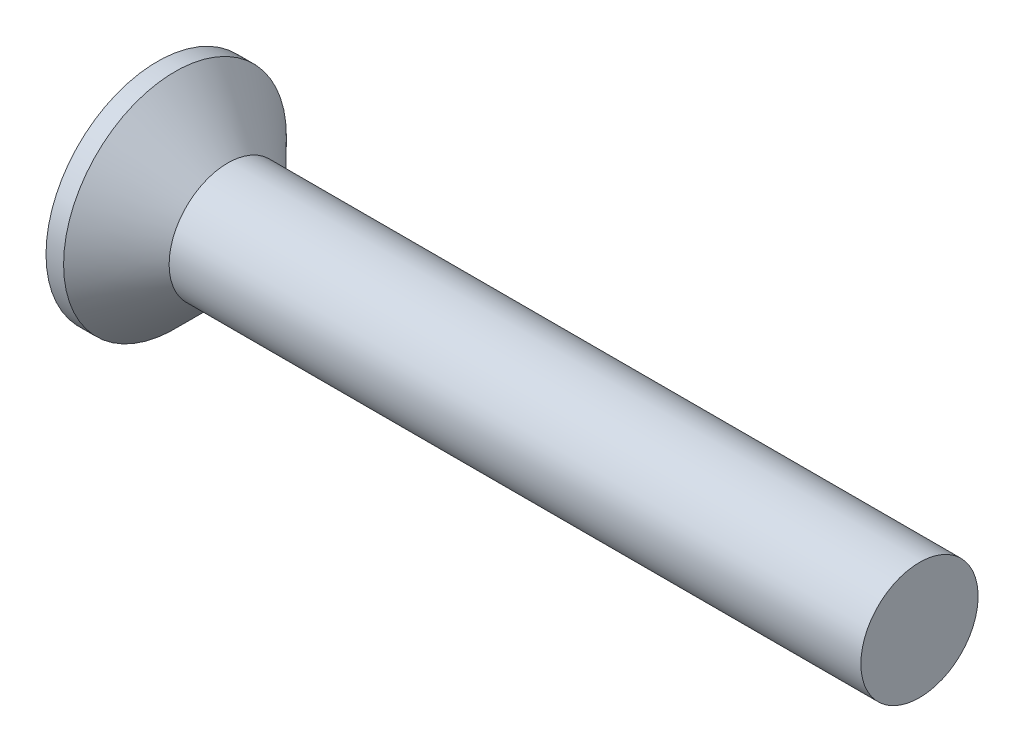
SolidWorks part; units mm, degrees
revolve "Base-Revolve" add sketch "BodySke" angle 360 about L5
sketch "BodySke" plane through (0, 0, 0) normal (0, 0, 1) x (1, 0, 0)
  line L0 (0, 0) -> (0, 1.9)
  line L1 (0, 1.9) -> (0.3, 1.9)
  line L2 (1.2, 1) -> (13, 1)
  line L3 (13, 1) -> (13, 0)
  line L4 (13, 0) -> (0, 0)
  line L5 (-6.35, 0) -> (82.55, 0) construction
  line L6 (1.2, -1) -> (13, -1) construction
  line L7 (0.3, -1.9) -> (1.2, -1) construction
  line L8 (0.3, 1.9) -> (1.2, 1)
  line L9 (0, -1.9) -> (0.3, -1.9) construction
  line L10 (1.6, 2.5875) -> (1.6, -6.9375) construction
  line L11 (0, 6.35) -> (0, -3.175) construction
  dimension "Diameter" = 2
  dimension "Length" = 13
  dimension "Head_ht" = 1.2
  dimension "Head_dia" = 3.8
  dimension "Head_ang" = 90
  dimension "D6" = 0.3
  dimension "Advance" = 0.4
  dimension "Thread_nom" = 13
cosmetic thread "ThreadCosmetic" parameters "Thread_length"=11.4, "Thread_minor"=1.548
extrude "Slot" [suppressed] cut sketch "Sketch2" against normal blind 0.6
sketch "Sketch2" plane through (0, 0, 0) normal (-1, 0, 0) x (0, 0, 1)
  line L0 (-1.9, -0.35) -> (1.9, -0.35)
  line L1 (-1.9, -0.35) -> (-1.9, 0.35)
  line L2 (1.9, 0.35) -> (-1.9, 0.35)
  line L3 (1.9, 0.35) -> (1.9, -0.35)
  dimension "Slot_width" = 0.7
  dimension "D1" = 0.35
  dimension "D2" = 3.8
  dimension "D3" = 1.9
ref_plane "Plane1" through (0, 0, 0) normal (0, 0, 1) x (1, 0, 0)
ref_plane "Plane2" through (0, 0, 0) normal (0, 1, 0) x (1, 0, 0)
ref_plane "Plane3" through (0, 0, 0) normal (1, 0, 0) x (0, 0, -1)
other "Configuration Table"
sketch "Sketch3" plane through (0, 0, 0) normal (-1, 0, 0) x (0, 0, 1)
  line L0 (-0.265, 1.07) -> (0.265, 1.07)
  line L1 (0.265, 1.07) -> (0.265, -1.07)
  line L2 (0.265, -1.07) -> (-0.265, -1.07)
  line L3 (-0.265, -1.07) -> (-0.265, 1.07)
  dimension "Cross_dia" = 2.14
  dimension "Cross_width" = 0.53
  dimension "D1" = 1.07
  dimension "D2" = 0.265
ref_plane "Plane4" through (1.54, 0, 0) normal (-1, 0, 0) x (0, 0, 1)
sketch "Sketch4" plane through (1.54, 0, 0) normal (-1, 0, 0) x (0, 0, 1)
  line L0 (-0.1325, 0.1325) -> (0.1325, 0.1325)
  line L3 (0.1325, 0.1325) -> (0.1325, -0.1325)
  line L4 (0.1325, -0.1325) -> (-0.1325, -0.1325)
  line L5 (-0.1325, -0.1325) -> (-0.1325, 0.1325)
  dimension "D2" = 0.265
  dimension "D1" = 0.265
  dimension "D3" = 0.1325
  dimension "D4" = 0.1325
loft "Cross" cut profiles "Sketch3", "Sketch4"
pattern_circular "CirPattern1" count 2 every 90 about axis through (0, 0, 0) along (1, 0, 0) of "Cross"
sketch "ThdSchSke" plane through (0, 0, 0) normal (0, 0, 1) x (1, 0, 0)
  line L0 (1.6, -0.774) -> (1.4418, -1)
  line L1 (1.6, -0.774) -> (1.7582, -1)
  line L2 (1.7582, -1) -> (1.7582, -1.25)
  line L3 (-3.175, 0) -> (5.1513, 0) construction
  line L5 (1.7582, -1.25) -> (1.4418, -1.25)
  line L6 (1.4418, -1.25) -> (1.4418, -1)
  line L7 (0, 1.9) -> (0, -1.9) construction
  dimension "Diameter" = 2
  dimension "Thread_minor" = 1.548
  dimension "Start" = 1.6
revolve "ThreadSchematic" [suppressed] cut sketch "ThdSchSke" angle 360 about L3
pattern_linear "ThdSchPat" [suppressed]
equation "\"D1@Sketch3\" = \"Cross_dia@Sketch3\" / 2"
equation "\"D2@Sketch3\" = \"Cross_width@Sketch3\" / 2"
equation "\"D1@Sketch4\" = \"Cross_width@Sketch3\" *.5"
equation "\"D2@Sketch4\" = \"D1@Sketch4\""
equation "\"D4@Sketch4\" = \"D2@Sketch4\" / 2"
equation "\"D3@Sketch4\" = \"D1@Sketch4\" / 2"
equation "\"D1@Sketch2\" = \"Slot_width@Sketch2\" / 2"
equation "\"D2@Sketch2\" = \"Head_dia@BodySke\""
equation "\"D3@Sketch2\" = \"D2@Sketch2\" / 2"
equation "\"Thread_length@ThreadCosmetic\" = ((sgn( (\"Length@BodySke\" - \"Advance@BodySke\" - \"Head_ht@BodySke\" ) - \"Thread_nom@BodySke\" )-1)*( (\"Length@BodySke\" - \"Advance@BodySke\" - \"Head_ht@BodySke\" ) - \"Thread_nom@BodySke\" ))/-2+ \"Thread_nom@BodySke\""
equation "\"Thread_minor@ThdSchSke\" = \"Thread_minor@ThreadCosmetic\""
equation "\"Diameter@ThdSchSke\" = \"Diameter@BodySke\""
equation "\"Overcut@ThdSchSke\" = \"Diameter@BodySke\" * 1.25"
equation "\"Start@ThdSchSke\" = 0.000001 + \"Length@BodySke\" - \"Thread_length@ThreadCosmetic\"  '---Countersunk---"
equation "\"Num_threads@ThdSchPat\" = int( \"Thread_length@ThreadCosmetic\" / \"Advance@BodySke\" + 0.999 )  + 1"
equation "\"Advance@ThdSchPat\" = \"Thread_length@ThreadCosmetic\" /  (\"Num_threads@ThdSchPat\" - 1) 'relax it"
